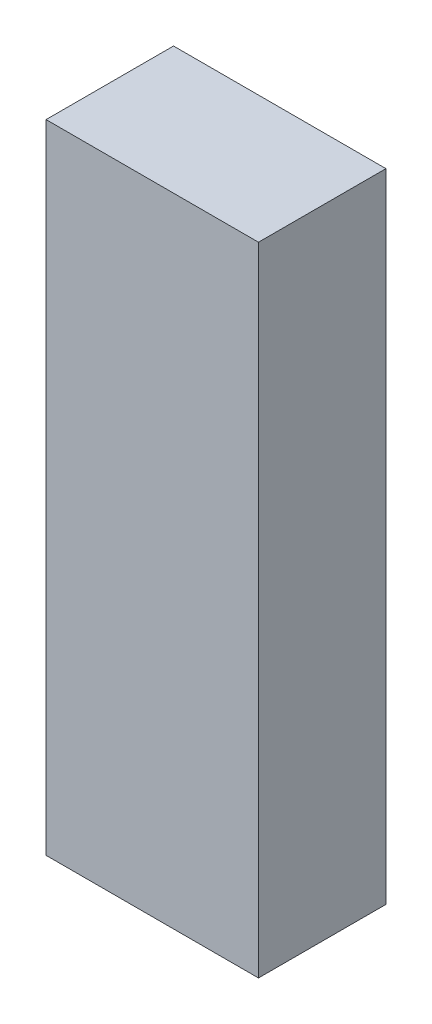
SolidWorks part; units mm, degrees
ref_plane "Front Plane" through (0, 0, 0) normal (0, 0, 1) x (1, 0, 0)
ref_plane "Top Plane" through (0, 0, 0) normal (0, 1, 0) x (1, 0, 0)
ref_plane "Right Plane" through (0, 0, 0) normal (1, 0, 0) x (0, 0, -1)
sketch "Sketch1" plane through (0, 0, 0) normal (0, 0, 1) x (1, 0, 0)
  line L1 (-313.7492, 0) -> (-273.7492, 0)
  line L2 (-313.7492, 0) -> (-313.7492, 120)
  line L3 (-313.7492, 120) -> (-273.7492, 120)
  line L4 (-273.7492, 0) -> (-273.7492, 120)
  dimension "D1" = 40
  dimension "D2" = 120
extrude "Boss-Extrude1" add sketch "Sketch1" along normal blind 24
